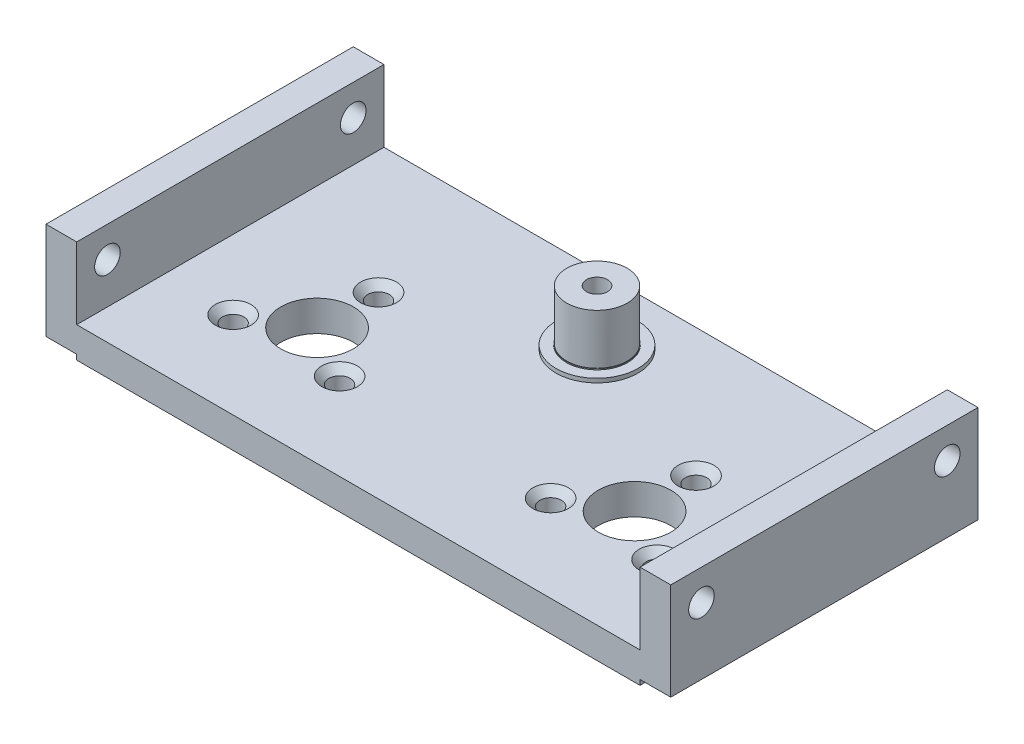
SolidWorks part; units mm, degrees
material "6061 Alloy"
ref_plane "Front Plane" through (0, 0, 0) normal (0, 0, 1) x (1, 0, 0)
ref_plane "Top Plane" through (0, 0, 0) normal (0, 1, 0) x (1, 0, 0)
ref_plane "Right Plane" through (0, 0, 0) normal (1, 0, 0) x (0, 0, -1)
sketch "Sketch1" plane through (0, 0, 0) normal (0, 1, 0) x (1, 0, 0)
  line L0 (55, 1) -> (0, 1)
  line L2 (0, 1) -> (0, 31)
  line L3 (0, 31) -> (55, 31)
  line L4 (55, 1) -> (55, 31)
  dimension "D1" = 30
extrude "Boss-Extrude1" add sketch "Sketch1" along normal blind 3
sketch "Sketch2" plane through (0, 3, 0) normal (0, 1, 0) x (1, 0, 0)
  line L0 (0, 1) -> (55, 1) construction
  circle A0 centre (27.5, 24.3) radius 2.95
  dimension "D1" = 5.9
  dimension "D2" = 23.3
extrude "Boss-Extrude2" add sketch "Sketch2" along normal blind 4.9
sketch "Sketch8" plane through (0, 3, 0) normal (0, 1, 0) x (1, 0, 0)
  line L0 (55, 1) -> (55, 31) construction
  circle A1 centre (43, 12.4678) radius 3.55
  circle A3 centre (27.5, 24.3) radius 2.95 construction
  point P0 (43, 12.4678)
  dimension "D3" = 7.1
  dimension "D1" = 19.5
  dimension "D2" = 12
extrude "Cut-Extrude2" cut sketch "Sketch8" against normal blind 6
ref_plane "Plane1" through (27.5, 0, 0) normal (1, 0, 0) x (0, 0, -1)
mirror "Mirror1" about plane through (27.5, 0, 0) normal (1, 0, 0) of "Cut-Extrude2"
sketch "Sketch10" plane through (0, 3, 0) normal (0, 1, 0) x (1, 0, 0)
  line L0 (55, 1) -> (58, 1)
  line L1 (55, 31) -> (58, 31)
  line L2 (55, 31) -> (55, 1)
  line L4 (58, 31) -> (58, 1)
extrude "Boss-Extrude3" add sketch "Sketch10" along normal blind 6.5 and the other way blind 3
sketch "Sketch11" plane through (0, 3, 0) normal (0, 1, 0) x (1, 0, 0)
  line L0 (0, 1) -> (-3, 1)
  line L1 (0, 31) -> (-3, 31)
  line L2 (0, 31) -> (0, 1)
  line L4 (-3, 31) -> (-3, 1)
extrude "Boss-Extrude4" add sketch "Sketch11" along normal blind 6.5 and the other way blind 3
hole_wizard "Tap Drill for M3x0.5 Tap1" positions "Sketch13" profile "Sketch12" hole size "M3x0.5" standard "ANSI Metric"
sketch "Sketch13" plane through (-3, 0, 0) normal (-1, 0, 0) x (0, 0, 1)
  line L2 (-1, 0) -> (-1, 9.5) construction
  line L3 (-31, 0) -> (-31, 9.5) construction
  line L4 (-31, 9.5) -> (-1, 9.5) construction
  point P0 (-28, 6.5)
  point P2 (-4, 6.5)
  dimension "D1" = 3
  dimension "D2" = 3
  dimension "D3" = 3
  dimension "D4" = 3
sketch "Sketch12" plane through (-3, 6.5, -28) normal (0, 1, 0) x (0, 0, 1)
  line L0 (0, 0) -> (0, 10.7511)
  line L1 (0, 10.7511) -> (1.25, 10)
  line L2 (1.25, 10) -> (1.25, 0)
  line L5 (1.25, 0) -> (0, 0)
  line L10 (0, 10.7511) -> (-1.25, 10) construction
  line L11 (0, -6.35) -> (0, 107.95) construction
  dimension "Hole Dia." = 2.5
  dimension "Hole Depth" = 10
  dimension "Drill Angle" = 118
mirror "Mirror2" about plane through (27.5, 0, 0) normal (1, 0, 0) of "Tap Drill for M3x0.5 Tap1"
sketch "Sketch15" plane through (0, 7.9, 0) normal (0, 1, 0) x (1, 0, 0)
  point P0 (27.5, 24.3)
hole_wizard "Tap Drill for M2.5x0.45 Tap2" positions "Sketch17" profile "Sketch16" hole size "M2.5x0.45" standard "ANSI Metric"
sketch "Sketch17" plane through (0, 7.9, 0) normal (0, 1, 0) x (1, 0, 0)
  point P0 (27.5, 24.3)
sketch "Sketch16" plane through (27.5, 7.9, -24.3) normal (1, 0, 0) x (0, 0, 1)
  line L0 (0, 0) -> (0, 6.6159)
  line L1 (0, 6.6159) -> (1.025, 6)
  line L2 (1.025, 6) -> (1.025, 0)
  line L5 (1.025, 0) -> (0, 0)
  line L10 (0, 6.6159) -> (-1.025, 6) construction
  line L11 (0, -6.35) -> (0, 107.95) construction
  dimension "Hole Dia." = 2.05
  dimension "Hole Depth" = 6
  dimension "Drill Angle" = 118
sketch "Sketch18" plane through (0, 3, 0) normal (0, 1, 0) x (1, 0, 0)
  circle A0 centre (12, 18.4678) radius 1.05
  circle A1 centre (43, 18.4678) radius 1.05
  circle A2 centre (12, 12.4678) radius 3.55 construction
  circle A3 centre (43, 12.4678) radius 3.55 construction
  dimension "D1" = 2.1
  dimension "D2" = 2.1
  dimension "D3" = 6
  dimension "D4" = 6
extrude "Cut-Extrude4" cut sketch "Sketch18" against normal blind 10 contours A0
pattern_circular "CirPattern2" count 3 over 360 about axis through (12, 0, -12.4678) along (0, 1, 0) of "Cut-Extrude4"
mirror "Mirror3" about plane through (27.5, 0, 0) normal (1, 0, 0) of "CirPattern2", "Cut-Extrude4"
sketch "Sketch21" plane through (0, 3, 0) normal (0, 1, 0) x (1, 0, 0)
  line L1 (55, 31) -> (0, 31)
  line L2 (55, 31) -> (55, 1)
  line L3 (55, 1) -> (0, 1)
  line L4 (0, 31) -> (0, 1)
  circle A0 centre (27.5, 24.3) radius 4
extrude "Cut-Extrude7" cut sketch "Sketch21" against normal blind 0.5
sketch "Sketch23" plane through (0, 3, 0) normal (0, 1, 0) x (1, 0, 0)
  circle A0 centre (27.5, 24.3) radius 4
  circle A1 centre (27.5, 24.3) radius 3
extrude "Cut-Extrude8" cut sketch "Sketch23" against normal blind 0.1
hole_wizard "CSK for M2 Flat Head Machine Screw1" positions "3DSketch1" profile "Sketch24" countersink size "M2" standard "ANSI Metric"
sketch3d "3DSketch1"
  line L0 (43, 0, -18.4678) -> (43, 2.5, -18.4678) construction
  line L1 (48.1962, 0, -9.4678) -> (48.1962, 2.5, -9.4678) construction
  line L2 (37.8038, 0, -9.4678) -> (37.8038, 2.5, -9.4678) construction
  line L3 (17.1962, 0, -9.4678) -> (17.1962, 2.5, -9.4678) construction
  line L4 (12, 0, -18.4678) -> (12, 2.5, -18.4678) construction
  line L5 (6.8038, 0, -9.4678) -> (6.8038, 2.5, -9.4678) construction
  point P0 (43, 2.5, -18.4678)
  point P4 (48.1962, 2.5, -9.4678)
  point P8 (37.8038, 2.5, -9.4678)
  point P12 (17.1962, 2.5, -9.4678)
  point P16 (12, 2.5, -18.4678)
  point P20 (6.8038, 2.5, -9.4678)
sketch "Sketch24" plane through (43, 2.5, -18.4678) normal (1, 0, 0) x (0, 0, 1)
  line L0 (0, 0) -> (0, 10.1309)
  line L1 (0, 10.1309) -> (1.05, 9.5)
  line L2 (1.05, 9.5) -> (1.05, 0.7)
  line L3 (1.05, 0.7) -> (1.75, 0)
  line L5 (1.75, 0) -> (0, 0)
  line L6 (-1.05, 0.7) -> (-1.75, 0) construction
  line L10 (0, 10.1309) -> (-1.05, 9.5) construction
  line L11 (0, -6.35) -> (0, 107.95) construction
  dimension "Hole Dia." = 2.1
  dimension "Hole Depth" = 9.5
  dimension "Near C'Sink Dia." = 3.5
  dimension "Near C'Sink Angle" = 90
  dimension "Drill Angle" = 118
sketch "Sketch25" plane through (0, 0, 0) normal (0, -1, 0) x (-1, 0, 0)
  line L1 (-55, 1) -> (0, 1)
  line L2 (-55, 1) -> (-55, 31)
  line L3 (-55, 31) -> (0, 31)
  line L4 (0, 1) -> (0, 31)
  circle A0 centre (-43, 12.4678) radius 3.55
  circle A1 centre (-48.1962, 9.4678) radius 1.05
  circle A2 centre (-43, 18.4678) radius 1.05
  circle A3 centre (-37.8038, 9.4678) radius 1.05
  circle A4 centre (-12, 12.4678) radius 3.55
  circle A5 centre (-17.1962, 9.4678) radius 1.05
  circle A6 centre (-12, 18.4678) radius 1.05
  circle A7 centre (-6.8038, 9.4678) radius 1.05
extrude "Boss-Extrude6" add sketch "Sketch25" along normal blind 0.5
